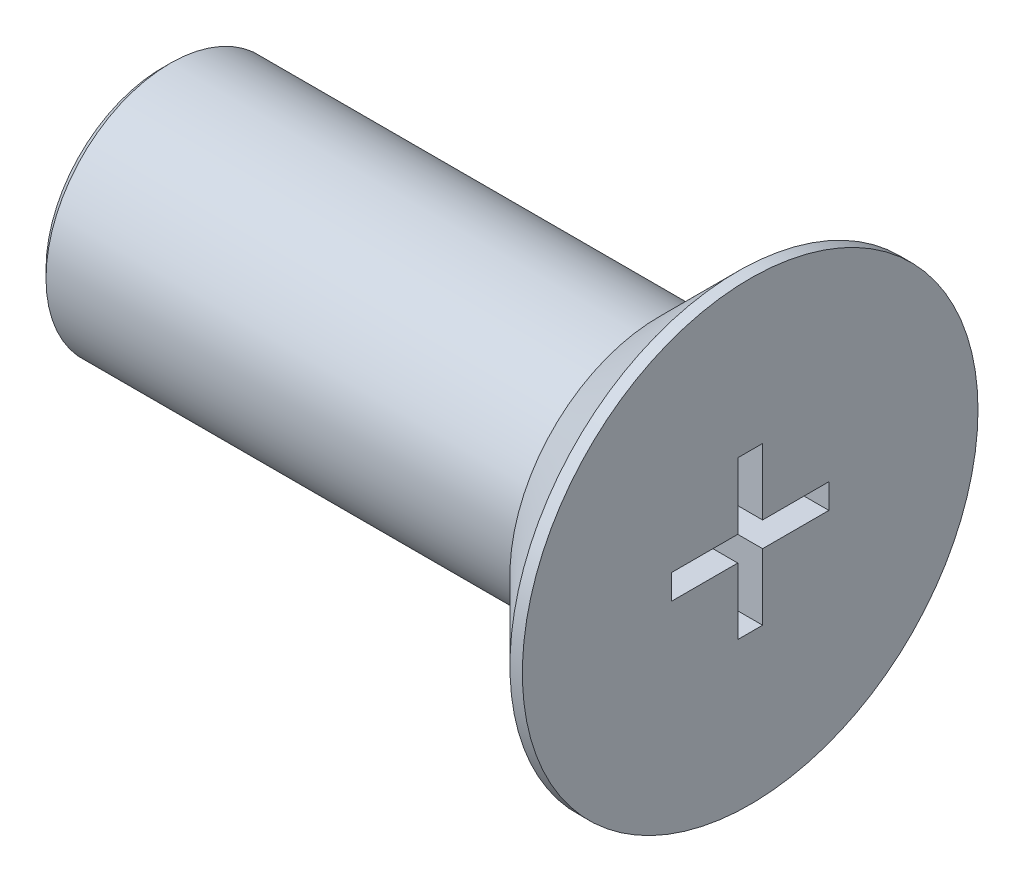
SolidWorks part; units mm, degrees
ref_plane "前视基准面" through (0, 0, 0) normal (0, 0, 1) x (1, 0, 0)
ref_plane "上视基准面" through (0, 0, 0) normal (0, 1, 0) x (1, 0, 0)
ref_plane "右视基准面" through (0, 0, 0) normal (1, 0, 0) x (0, 0, -1)
sketch "草图1" plane through (0, 0, 0) normal (1, 0, 0) x (0, 0, -1)
  circle A0 centre (0, 0) radius 5.5
  dimension "D1" = 11
extrude "凸台-拉伸1" add sketch "草图1" along normal blind 2.2
sketch "草图2" plane through (0, 0, 0) normal (-1, 0, 0) x (0, 0, 1)
  circle A0 centre (0, 0) radius 3
  dimension "D1" = 6
extrude "凸台-拉伸3" add sketch "草图2" along normal blind 12
cosmetic thread "装饰螺纹线2" parameters "D2"=4
chamfer "倒角2" distance 0.2 angle 45 1 edges at (-12, 0, 3)
chamfer "倒角3" distance 1.9 angle 45 1 edges at (0, 0, -5.5)
sketch "草图5" plane through (2.2, 0, 0) normal (1, 0, 0) x (0, 0, -1)
  line L0 (0.3, 0.3) -> (1.9, 0.3)
  line L1 (1.9, 0.3) -> (1.9, -0.3)
  line L2 (1.9, -0.3) -> (0.3, -0.3)
  line L3 (0.3, -0.3) -> (0.3, -1.9)
  line L4 (0.3, -1.9) -> (-0.3, -1.9)
  line L5 (-0.3, -1.9) -> (-0.3, -0.3)
  line L6 (-0.3, -0.3) -> (-1.9, -0.3)
  line L7 (-1.9, -0.3) -> (-1.9, 0.3)
  line L8 (-1.9, 0.3) -> (-0.3, 0.3)
  line L9 (-0.3, 0.3) -> (-0.3, 1.9)
  line L10 (-0.3, 1.9) -> (0.3, 1.9)
  line L11 (0.3, 1.9) -> (0.3, 0.3)
  dimension "D1" = 0.6
  dimension "D2" = 0.6
  dimension "D3" = 0.6
  dimension "D4" = 0.6
  dimension "D5" = 0.3
  dimension "D6" = 0.3
  dimension "D7" = 0.3
  dimension "D8" = 0.3
  dimension "D9" = 1.6
  dimension "D10" = 1.6
  dimension "D11" = 1.6
  dimension "D12" = 1.6
extrude "切除-拉伸2" cut sketch "草图5" against normal blind 3
